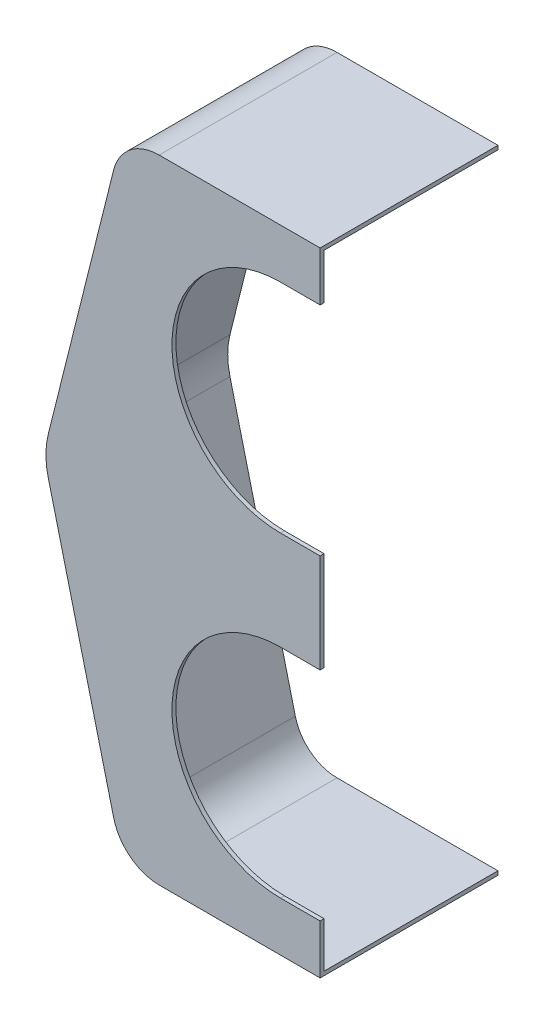
SolidWorks part; units mm, degrees
material "ABS PC"
ref_plane "Front Plane" through (0, 0, 0) normal (0, 0, 1) x (1, 0, 0)
ref_plane "Top Plane" through (0, 0, 0) normal (0, 1, 0) x (1, 0, 0)
ref_plane "Right Plane" through (0, 0, 0) normal (1, 0, 0) x (0, 0, -1)
sketch "Sketch1" plane through (0, 0, 0) normal (1, 0, 0) x (0, 0, -1)
  line L1 (0, 0) -> (114.3, 0)
  line L2 (0, 0) -> (0, -203.2)
  line L3 (0, -203.2) -> (114.3, -203.2)
  line L4 (114.3, 0) -> (114.3, -203.2)
  point P4 (-54.5201, 88.1278)
  point P5 (0, 0)
  point P6 (0, 0)
  dimension "D1" = 203.2
  dimension "D2" = 114.3
extrude "Boss-Extrude1" add sketch "Sketch1" against normal blind 88.9
sketch "Sketch4" plane through (0, 0, -114.3) normal (0, 0, -1) x (-1, 0, 0)
  line L0 (63.5, 0) -> (88.9, -101.6)
  line L1 (88.9, -101.6) -> (63.5, -203.2)
  line L2 (48.895, 0) -> (-48.895, 0) construction
  line L3 (88.9, -203.2) -> (0, -203.2) construction
  line L4 (88.9, -203.2) -> (88.9, 0) construction
  line L9 (63.5, 0) -> (88.9, 0)
  line L10 (88.9, 0) -> (88.9, -203.2)
  line L11 (88.9, -203.2) -> (63.5, -203.2)
  point P2 (0, 0)
  point P10 (63.8114, -201.9545)
  point P13 (88.9, -101.6)
  point P14 (0, 0)
  point P15 (0, 0)
  point P19 (0, 0)
  point P20 (88.9, 0)
  point P21 (85.4907, 0)
  line M6 (0, -203.2) -> (88.9, -203.2)
  line M7 (88.9, -203.2) -> (88.9, 0)
  line M8 (88.9, 0) -> (0, 0)
  dimension "D1" = 25.4
  dimension "D2" = 25.4
extrude "Cut-Extrude1" cut sketch "Sketch4" against normal through all contours L0 M8 M7 | L1 M7 M6
fillet "Fillet1" radius 25.24 1 edges at (-88.9, -101.6, -57.15)
fillet "Fillet2" radius 15.08 2 edges at (-63.5, 0, -57.15) (-63.5, -203.2, -57.15)
sketch "Sketch5" plane through (0, 0, 0) normal (0, 0, 1) x (1, 0, 0)
  line L0 (-60.5871, -101.6) -> (-23.5513, -101.6) construction
  line L1 (0, 0) -> (0, -203.2) construction
  line L2 (-12.7, -187.325) -> (0, -187.325)
  line L3 (-12.7, -117.475) -> (0, -117.475)
  line L4 (0, -187.325) -> (0, -117.475)
  arc A0 (-12.7, -117.475) -> (-12.7, -187.325) centre (-12.7, -152.4) ccw
  point P4 (0, -101.6)
  dimension "D3" = 69.85
  dimension "D1" = 50.8
  dimension "D2" = 12.7
extrude "Cut-Extrude2" cut sketch "Sketch5" against normal through all
pattern_linear "LPattern1" count 2 spacing 101.6 along (0, 1, 0) of "Cut-Extrude2"
shell "Shell5" thickness 1.27
sketch "Sketch9" plane through (0, 0, -113.03) normal (0, 0, 1) x (1, 0, 0)
  line L0 (0, -117.475) -> (0, -85.725) construction
  circle A0 centre (-12.7, -101.6) radius 3
  point P4 (0, -101.6)
  point P5 (-12.1307, -111.1178)
  point P6 (0, 0)
  dimension "D1" = 12.7
extrude "Boss-Extrude2" add sketch "Sketch9" along normal blind 8.89
ref_plane "Plane1" through (0, 0, -57.15) normal (0, 0, 1) x (1, 0, 0)
mirror "Mirror1" about plane through (0, 0, -57.15) normal (0, 0, 1) of "Boss-Extrude2"
sketch "Sketch10" plane through (0, 0, 0) normal (0, 1, 0) x (1, 0, 0)
  line L0 (-48.4678, 57.15) -> (48.4678, 57.15) construction
  line L1 (-88.1232, 114.3) -> (0, 114.3)
  line L2 (-88.1232, 114.3) -> (-88.1232, 57.15)
  line L3 (-88.1232, 57.15) -> (0, 57.15)
  line L4 (0, 114.3) -> (0, 57.15)
  line L5 (-88.1232, 114.3) -> (-88.1232, 0) construction
  line L6 (0, -62.865) -> (0, 62.865) construction
  dimension "D1" = 57.15
extrude "Cut-Extrude3" cut sketch "Sketch10" against normal through all
